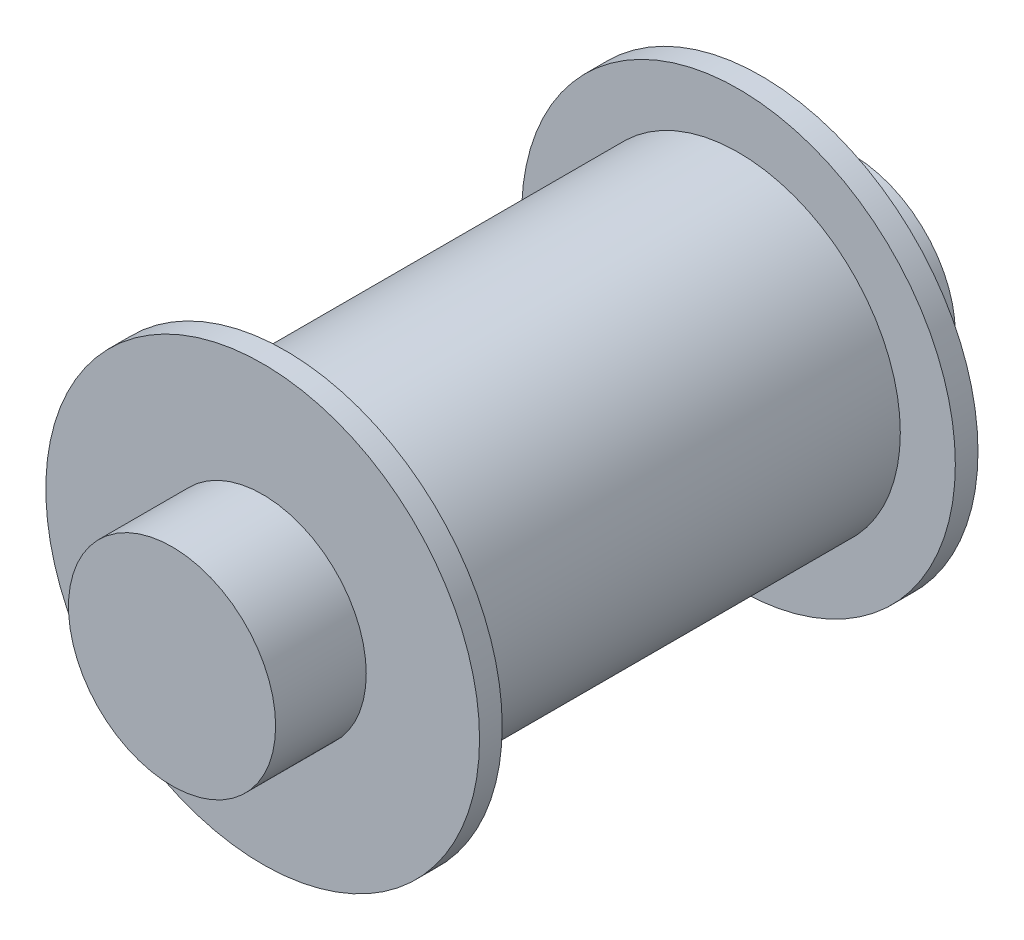
SolidWorks part; units mm, degrees
material "AISI 304"
ref_plane "Front Plane" through (0, 0, 0) normal (0, 0, 1) x (1, 0, 0)
ref_plane "Top Plane" through (0, 0, 0) normal (0, 1, 0) x (1, 0, 0)
ref_plane "Right Plane" through (0, 0, 0) normal (1, 0, 0) x (0, 0, -1)
sketch "Sketch1" plane through (0, 0, 0) normal (1, 0, 0) x (0, 0, -1)
  line L0 (-38.5, 0) -> (38.5, 0)
  line L1 (-38.5, -33.5) -> (-38.5, 33.5) construction
  line L2 (-38.5, 33.5) -> (-35, 33.5)
  line L3 (38.5, 33.5) -> (38.5, -33.5) construction
  line L4 (-38.5, -33.5) -> (-35, -33.5) construction
  line L5 (0, 0) -> (0, 25) construction
  line L6 (38.5, 16) -> (38.5, 33.5)
  line L7 (-38.5, -33.5) -> (-38.5, 33.5) construction
  line L8 (0, 0) -> (38.5, 0) construction
  line L9 (-35, 33.5) -> (-35, 25)
  line L10 (-35, 25) -> (35, 25)
  line L11 (35, 25) -> (35, 33.5)
  line L12 (35, 33.5) -> (38.5, 33.5)
  line L13 (35, -33.5) -> (38.5, -33.5) construction
  line L14 (35, -25) -> (35, -33.5) construction
  line L15 (-35, -25) -> (35, -25) construction
  line L16 (-35, -33.5) -> (-35, -25) construction
  line L17 (38.5, 0) -> (38.5, -33.5) construction
  line L18 (-38.5, -33.5) -> (-35, -33.5) construction
  line L19 (-38.5, 16) -> (-38.5, 33.5)
  line L20 (35, -33.5) -> (38.5, -33.5) construction
  line L21 (38.5, 16) -> (52.5, 16)
  line L22 (52.5, 16) -> (52.5, -16) construction
  line L23 (52.5, 0) -> (38.5, 0)
  line L24 (-52.5, 0) -> (-38.5, 0)
  line L25 (-52.5, 16) -> (-52.5, -16) construction
  line L26 (-38.5, 16) -> (-52.5, 16)
  line L27 (-38.5, -16) -> (-52.5, -16) construction
  line L28 (38.5, -16) -> (52.5, -16) construction
  line L29 (-52.5, 0) -> (-52.5, 16)
  line L30 (52.5, 0) -> (52.5, 16)
  point P9 (-38.5, 0)
  dimension "D1" = 67
  dimension "D2" = 77
  dimension "D3" = 3.5
  dimension "D4" = 3.5
  dimension "D5" = 25
  dimension "D6" = 16
  dimension "D7" = 14
revolve "Revolve1" add sketch "Sketch1" angle 360 about L8
